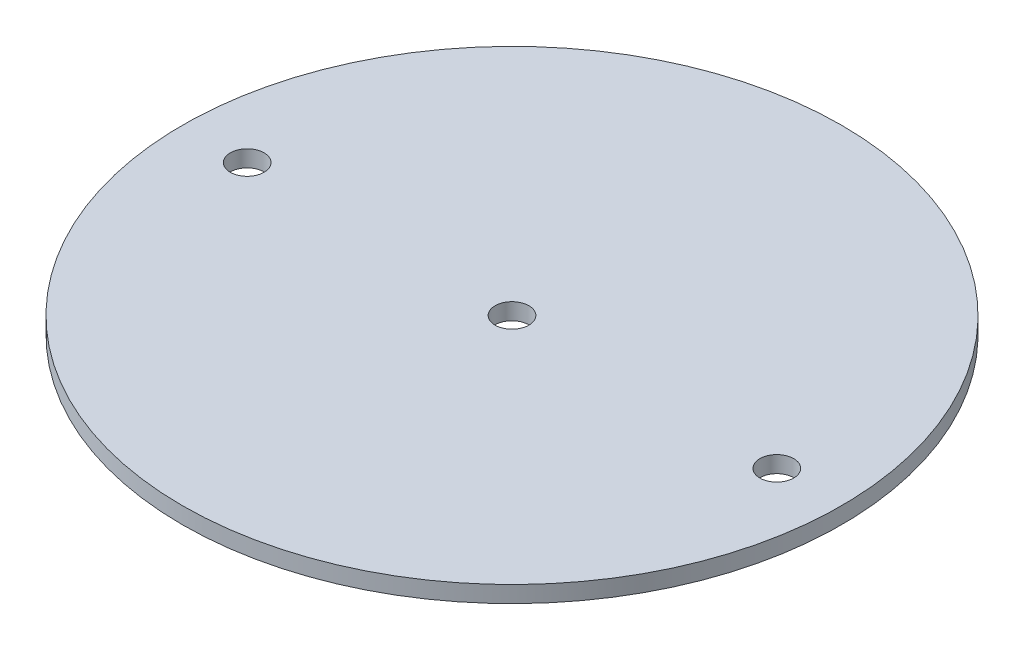
SolidWorks part; units mm, degrees
ref_plane "Front Plane" through (0, 0, 0) normal (0, 0, 1) x (1, 0, 0)
ref_plane "Top Plane" through (0, 0, 0) normal (0, 1, 0) x (1, 0, 0)
ref_plane "Right Plane" through (0, 0, 0) normal (1, 0, 0) x (0, 0, -1)
sketch "Sketch2" plane through (0, 0, 0) normal (0, 1, 0) x (1, 0, 0)
  line L0 (-50.8, 0) -> (50.8, 0) construction
  circle A0 centre (0, 0) radius 63.2206
  circle A1 centre (-50.8, 0) radius 3.2385
  circle A2 centre (50.8, 0) radius 3.2385
  circle A3 centre (0, 0) radius 3.2385
  point P6 (0, 0)
  dimension "D1" = 126.4412
  dimension "D3" = 6.477
  dimension "D4" = 6.477
  dimension "D2" = 101.6
extrude "Boss-Extrude1" add sketch "Sketch2" along normal blind 3.175
